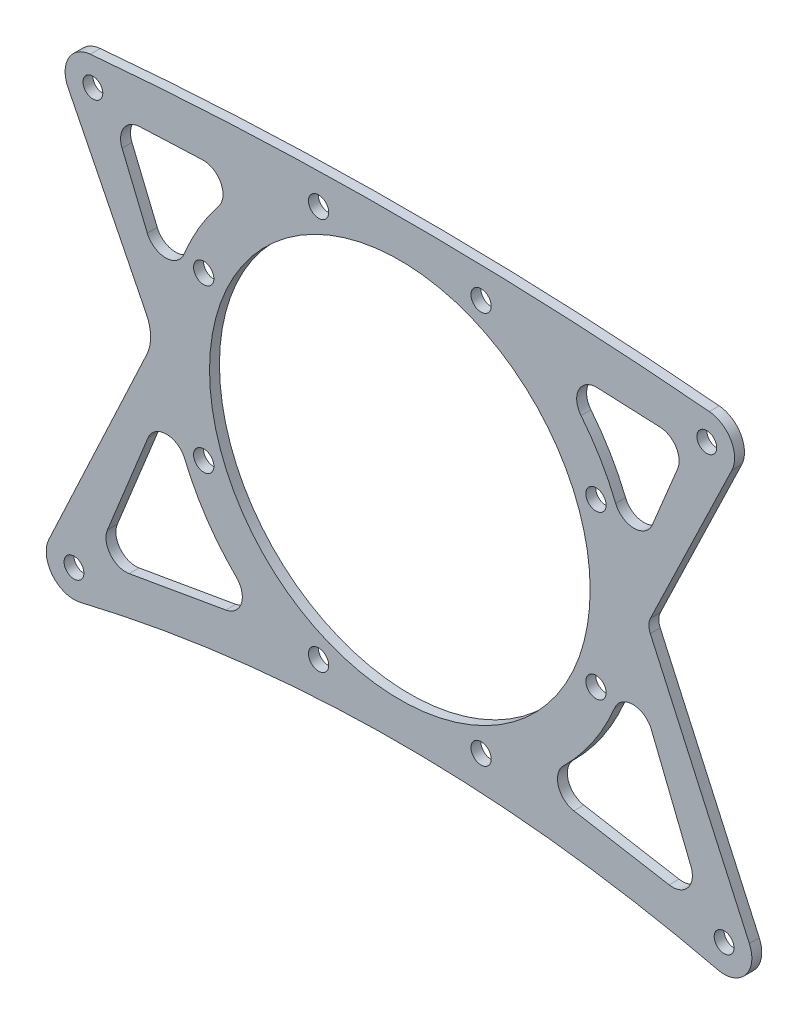
SolidWorks part; units mm, degrees
material "6061-T6 (SS)"
ref_plane "Front Plane" through (0, 0, 0) normal (0, 0, 1) x (1, 0, 0)
ref_plane "Top Plane" through (0, 0, 0) normal (0, 1, 0) x (1, 0, 0)
ref_plane "Right Plane" through (0, 0, 0) normal (1, 0, 0) x (0, 0, -1)
sketch "Sketch5" plane through (0, 0, 0) normal (0, 0, 1) x (1, 0, 0)
  line L0 (179.7268, -49.4259) -> (252.0316, -52.5593) construction
  line L1 (233.9351, -114.7635) -> (265.6657, -184.8836)
  line L2 (233.9872, -110.4632) -> (260.0397, -56.4197)
  line L3 (72.532, -106.8604) -> (47.4221, -56.5279)
  line L4 (179.7268, -175.0735) -> (257.5664, -188.5487) construction
  line L5 (55.3771, -52.5593) -> (127.6819, -49.4259) construction
  line L6 (41.2769, -184.9574) -> (72.6693, -117.9154)
  line L7 (49.3279, -188.7273) -> (127.6819, -175.0735) construction
  line L8 (209.4616, -176.1616) -> (239.9726, -181.4435)
  line L9 (234.2631, -141.1917) -> (246.9494, -172.8227)
  line L10 (216.9712, -55.0437) -> (237.0859, -55.9153)
  line L11 (242.6776, -64.6894) -> (234.5865, -84.2231)
  line L12 (49.3279, -188.7273) -> (90.8806, -86.2272) construction
  line L13 (55.3771, -52.5593) -> (90.8806, -138.2722) construction
  line L14 (252.0316, -52.5593) -> (216.5282, -138.2722) construction
  line L15 (216.5282, -86.2272) -> (257.5664, -188.5487) construction
  line L16 (67.0179, -181.5844) -> (97.9827, -176.1886)
  line L17 (60.0429, -172.9431) -> (73.0373, -140.889)
  line L18 (70.3229, -55.9153) -> (90.4375, -55.0437)
  line L19 (64.7312, -64.6894) -> (72.8223, -84.2231)
  line L20 (61.2595, -56.3081) -> (127.8551, -53.4221) construction
  line L21 (55.7433, -183.5491) -> (94.5875, -87.73) construction
  line L22 (55.7433, -183.5491) -> (126.9952, -171.1329) construction
  line L23 (180.4092, -171.1321) -> (251.1855, -183.3846) construction
  line L24 (61.2595, -56.3081) -> (94.5761, -136.7414) construction
  line L25 (212.8156, -87.7162) -> (251.1855, -183.3846) construction
  line L26 (246.1492, -56.3081) -> (212.8327, -136.7414) construction
  line L27 (179.5537, -53.4221) -> (246.1492, -56.3081) construction
  line L28 (153.7044, -112.2497) -> (90.8806, -86.2272) construction
  line L29 (90.8806, -86.2272) -> (20.0062, -257.3332) construction
  line L30 (153.7044, -112.2497) -> (90.8806, -138.2722) construction
  line L31 (90.8806, -138.2722) -> (13.272, 49.0915) construction
  line L32 (153.7044, -112.2497) -> (127.6819, -175.0735) construction
  line L33 (127.6819, -175.0735) -> (318.5674, -254.1409) construction
  line L34 (153.7044, -112.2497) -> (179.7268, -175.0735) construction
  line L35 (179.7268, -175.0735) -> (-36.5033, -264.639) construction
  line L36 (153.7044, -112.2497) -> (216.5282, -138.2722) construction
  line L37 (216.5282, -138.2722) -> (288.3269, 35.0652) construction
  line L38 (153.7044, -112.2497) -> (216.5282, -86.2272) construction
  line L39 (216.5282, -86.2272) -> (280.8434, -241.498) construction
  line L40 (153.7044, -112.2497) -> (179.7268, -49.4259) construction
  line L42 (153.7044, -112.2497) -> (127.6819, -49.4259) construction
  line L43 (127.6819, -49.4259) -> (318.7771, 29.7283) construction
  line L45 (179.7268, -49.4259) -> (0.1567, 24.9545) construction
  circle A0 centre (49.3279, -188.7273) radius 3.175
  arc A1 (84.7874, -140.8413) -> (101.3484, -165.4087) centre (153.7044, -112.2497) ccw
  circle A2 centre (55.3771, -52.5593) radius 3.175
  circle A3 centre (252.0316, -52.5593) radius 3.175
  circle A4 centre (90.8806, -138.2722) radius 3.25
  circle A5 centre (127.6819, -175.0735) radius 3.25
  circle A6 centre (179.7268, -175.0735) radius 3.25
  circle A7 centre (216.5282, -138.2722) radius 3.25
  circle A8 centre (216.5282, -86.2272) radius 3.25
  circle A9 centre (179.7268, -49.4259) radius 3.25
  circle A10 centre (127.6819, -49.4259) radius 3.25
  circle A11 centre (90.8806, -86.2272) radius 3.25
  circle A12 centre (153.7044, -112.2497) radius 60.96
  circle A13 centre (49.3279, -188.7273) radius 8.89 construction
  arc A14 (54.5796, -43.7051) -> (47.4221, -56.5279) centre (55.3771, -52.5593) ccw
  arc A15 (41.2769, -184.9574) -> (51.4033, -197.3717) centre (49.3279, -188.7273) ccw
  arc A16 (51.4033, -197.3717) -> (255.5059, -197.1966) centre (153.8206, -623.9661) cw
  arc A17 (255.5059, -197.1966) -> (265.6657, -184.8836) centre (257.5664, -188.5487) ccw
  arc A18 (233.9872, -110.4632) -> (233.9351, -114.7635) centre (238.5633, -112.6692) ccw
  arc A19 (260.0397, -56.4197) -> (252.8292, -43.7051) centre (252.0316, -52.5593) ccw
  circle A20 centre (55.3771, -52.5593) radius 3.175 construction
  arc A21 (72.532, -106.8604) -> (72.6693, -117.9154) centre (61.1677, -112.5298) cw
  circle A22 centre (257.5664, -188.5487) radius 8.89 construction
  circle A23 centre (55.3771, -52.5593) radius 8.89 construction
  arc A24 (234.2631, -141.1917) -> (222.5134, -141.1001) centre (228.3695, -143.5554) ccw
  arc A25 (239.9726, -181.4435) -> (246.9494, -172.8227) centre (241.0558, -175.1865) ccw
  arc A26 (206.0867, -165.3827) -> (209.4616, -176.1616) centre (210.5448, -169.9046) ccw
  circle A27 centre (252.0316, -52.5593) radius 3.175 construction
  circle A28 centre (252.0316, -52.5593) radius 8.89 construction
  arc A29 (95.653, -65.3769) -> (84.5725, -84.1818) centre (153.7044, -112.2497) ccw
  circle A30 centre (257.5664, -188.5487) radius 3.175
  circle A31 centre (257.5664, -188.5487) radius 3.175 construction
  circle A32 centre (49.3279, -188.7273) radius 3.175 construction
  arc A33 (237.0859, -55.9153) -> (242.6776, -64.6894) centre (236.8109, -62.2594) cw
  circle A34 centre (90.8806, -138.2722) radius 3.25 construction
  circle A35 centre (90.8806, -138.2722) radius 6.5 construction
  arc A36 (54.5796, -43.7051) -> (252.8292, -43.7051) centre (153.7044, -1144.1503) cw
  circle A37 centre (153.7044, -112.2497) radius 73 construction
  arc A38 (72.8223, -84.2231) -> (84.5725, -84.1818) centre (78.6889, -81.7931) ccw
  arc A39 (77.7877, -106.6632) -> (77.8321, -118.4146) centre (80.2177, -112.5298) ccw construction
  arc A40 (60.0429, -172.9431) -> (67.0179, -181.5844) centre (65.9278, -175.3287) ccw
  arc A41 (234.5865, -84.2231) -> (222.8363, -84.1818) centre (228.7198, -81.7931) cw
  arc A42 (216.9712, -55.0437) -> (211.7558, -65.3769) centre (216.6963, -61.3877) ccw
  arc A46 (64.7312, -64.6894) -> (70.3229, -55.9153) centre (70.5978, -62.2594) cw
  arc A51 (95.653, -65.3769) -> (90.4375, -55.0437) centre (90.7124, -61.3877) ccw
  arc A53 (84.7874, -140.8413) -> (73.0373, -140.889) centre (78.9222, -143.2747) ccw
  arc A55 (97.9827, -176.1886) -> (101.3484, -165.4087) centre (96.8926, -169.9328) ccw
  arc A61 (206.0867, -165.3827) -> (222.5134, -141.1001) centre (153.7044, -112.2497) ccw
  arc A62 (222.8363, -84.1818) -> (211.7558, -65.3769) centre (153.7044, -112.2497) ccw
  arc A63 (228.0477, -106.3854) -> (233.3289, -114.0611) centre (227.1333, -112.6692) cw construction
  point P132 (80.2177, -112.5298)
  point P147 (227.1333, -112.6692)
  dimension "D1" = 13
  dimension "D2" = 12.7
  dimension "D3" = 5.08
  dimension "D5" = 4
  dimension "D6" = 4
  dimension "D7" = 4
  dimension "D8" = 6.35
  dimension "D9" = 6.35
  dimension "D10" = 6.35
  dimension "D11" = 6.35
  dimension "D12" = 121.92
  dimension "D13" = 74.6125
  dimension "D14" = 74.6125
  dimension "D15" = 6.35
  dimension "D4" = 4
extrude "Boss-Extrude2" add sketch "Sketch5" along normal blind 3.175 separate body
sketch "Stock" plane through (0, 0, 3.175) normal (0, 0, 1) x (1, 0, 0)
  line L1 (37.2629, -200.7923) -> (266.4564, -200.7923)
  line L2 (37.2629, -200.7923) -> (37.2629, -39.2497)
  line L3 (37.2629, -39.2497) -> (266.4564, -39.2497)
  line L4 (266.4564, -200.7923) -> (266.4564, -39.2497)
  arc A1 (255.5059, -197.1966) -> (265.6657, -184.8836) centre (257.5664, -188.5487) ccw construction
  arc A2 (252.8292, -43.7051) -> (54.5796, -43.7051) centre (153.7044, -1144.1503) ccw construction
  circle A3 centre (49.3279, -188.7273) radius 3.175 construction
  dimension "D1" = 12.065
  dimension "D2" = 12.065
  dimension "D3" = 161.5426
  dimension "D4" = 229.1934
